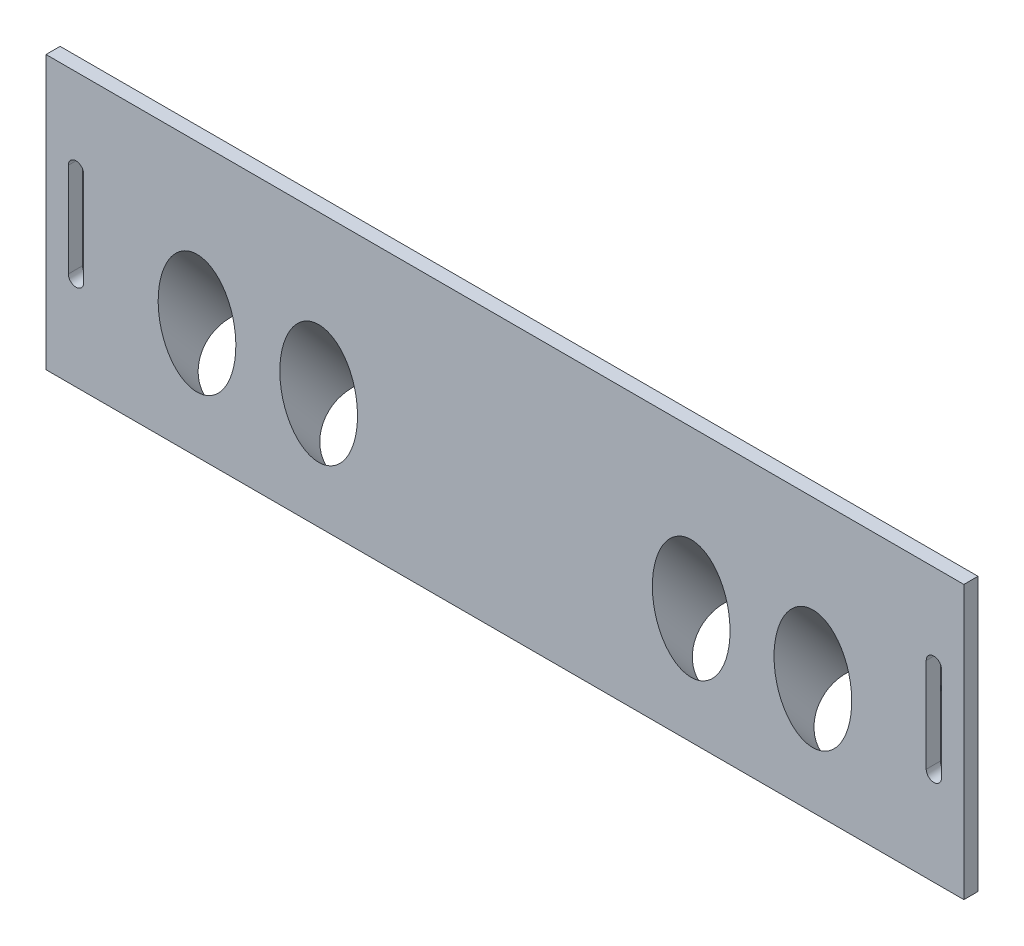
SolidWorks part; units mm, degrees
ref_plane "Alzado" through (0, 0, 0) normal (0, 0, 1) x (1, 0, 0)
ref_plane "Planta" through (0, 0, 0) normal (0, 1, 0) x (1, 0, 0)
ref_plane "Vista lateral" through (0, 0, 0) normal (1, 0, 0) x (0, 0, -1)
sketch "Croquis1" plane through (0, 0, 0) normal (0, 0, 1) x (1, 0, 0)
  line L0 (-97.5, 0) -> (97.5, 0)
  line L1 (97.5, 0) -> (97.5, 38)
  line L2 (97.5, 38) -> (-97.5, 38)
  line L3 (0, 0) -> (0, 28.0598) construction
  line L4 (-97.5, 0) -> (-97.5, 38)
  circle A2 centre (91.125, 15) radius 1.625
  circle A3 centre (-91.125, 15) radius 1.625
  point P13 (0, 38)
  point P14 (0, 0)
  dimension "D1" = 3.25
  dimension "D2" = 15
  dimension "D3" = 97.5
  dimension "D4" = 38
  dimension "D5" = 6.375
extrude "Saliente-Extruir1" add sketch "Croquis1" along normal blind 3
sketch "Croquis2" plane through (97.5, 0, 0) normal (1, 0, 0) x (0, 0, -1)
  line L7 (3.4296, 3.6779) -> (15.1854, 13.7539)
  line L9 (0, 0) -> (0, 38) construction
  line L10 (-3, 0) -> (0, 0) construction
  line L11 (15.1854, 13.7539) -> (0, 31.471)
  line L12 (0, 31.471) -> (0, 0.7384)
  line L13 (3.4296, 3.6779) -> (0, 0.7384)
  dimension "D1" = 40.6
  dimension "D2" = 20
extrude "Saliente-Extruir2" add sketch "Croquis2" along normal blind 45 from offset 67.5 offset against normal yes
sketch "Croquis4" plane through (-97.5, 0, 0) normal (-1, 0, 0) x (0, 0, 1)
  line L0 (0, 0.7384) -> (-15.1854, 13.7539)
  line L1 (-15.1854, 13.7539) -> (0, 31.471)
  line L2 (0, 38) -> (0, 0) construction
  line L3 (0, 0.7384) -> (0, 31.471) construction
  line L4 (0, 31.471) -> (0, 0.7384)
extrude "Saliente-Extruir3" add sketch "Croquis4" along normal blind 45 from offset 67.5 offset against normal yes
sketch "Croquis8" plane through (0, 0, 0) normal (0, -1, 0) x (1, 0, 0)
  line L1 (-97.5, 3) -> (97.5, 3)
  line L2 (-97.5, 3) -> (-97.5, 0)
  line L3 (-97.5, 0) -> (97.5, 0)
  line L4 (97.5, 3) -> (97.5, 0)
extrude "Saliente-Extruir5" add sketch "Croquis8" along normal blind 5
sketch "Croquis9" plane through (0, 0.4257, 0.3649) normal (0, -0.7593, -0.6508) x (1, 0, 0)
  line L1 (-75, -0.4805) -> (-75, -20.4805) construction
  line L2 (0, 5.5317) -> (0, -24.7294) construction
  line L3 (97.5, 5.5317) -> (-97.5, 5.5317) construction
  line L4 (97.5, -24.7294) -> (-97.5, -24.7294) construction
  circle A0 centre (-65.42, -10.4805) radius 8.25
  circle A1 centre (-39.57, -10.4805) radius 8.25
  circle A4 centre (39.57, -10.4805) radius 8.25
  circle A5 centre (65.42, -10.4805) radius 8.25
  dimension "D1" = 16.5
  dimension "D2" = 16.5
  dimension "D3" = 25.85
  dimension "D5" = 9.58
extrude "Cortar-Extruir4" cut sketch "Croquis9" against normal through all
sketch "Croquis10" plane through (0, 38, 0) normal (0, 1, 0) x (1, 0, 0)
  line L1 (-97.5, 0) -> (97.5, 0)
  line L2 (-97.5, 0) -> (-97.5, -3)
  line L3 (-97.5, -3) -> (97.5, -3)
  line L4 (97.5, 0) -> (97.5, -3)
extrude "Saliente-Extruir6" add sketch "Croquis10" along normal blind 15
sketch "Croquis11" plane through (0, 0, 0) normal (0, 0, -1) x (-1, 0, 0)
  line L0 (-92.75, 15) -> (-92.75, 35)
  line L1 (-89.5, 35) -> (-89.5, 15)
  line L2 (0, 0) -> (0, 73.356) construction
  line L3 (89.5, 35) -> (89.5, 15)
  line L4 (92.75, 15) -> (92.75, 35)
  arc A0 (-92.75, 15) -> (-89.5, 15) centre (-91.125, 15) ccw
  arc A1 (-89.5, 35) -> (-92.75, 35) centre (-91.125, 35) ccw
  arc A2 (89.5, 35) -> (92.75, 35) centre (91.125, 35) cw
  arc A3 (92.75, 15) -> (89.5, 15) centre (91.125, 15) cw
  dimension "D1" = 3.25
  dimension "D2" = 20
extrude "Cortar-Extruir5" cut sketch "Croquis11" against normal blind 15
